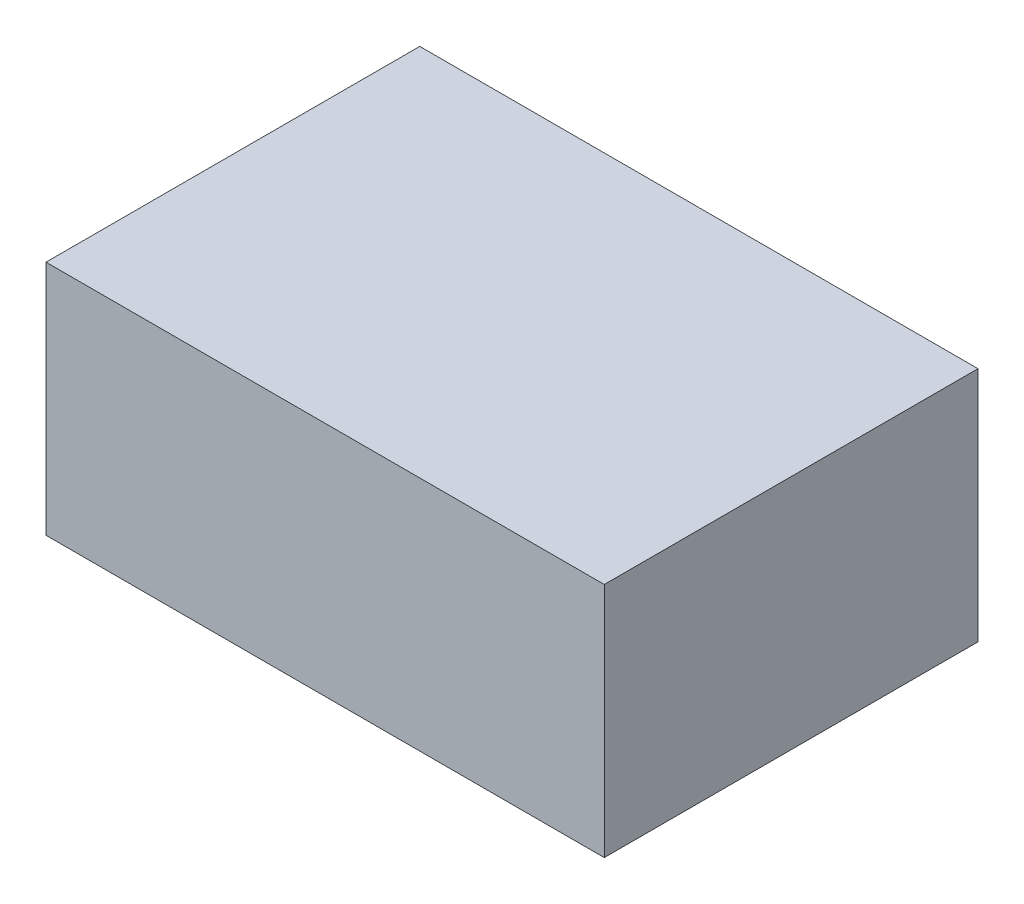
SolidWorks part; units mm, degrees
ref_plane "Front Plane" through (0, 0, 0) normal (0, 0, 1) x (1, 0, 0)
ref_plane "Top Plane" through (0, 0, 0) normal (0, 1, 0) x (1, 0, 0)
ref_plane "Right Plane" through (0, 0, 0) normal (1, 0, 0) x (0, 0, -1)
sketch "Sketch1" plane through (0, 0, 0) normal (0, 1, 0) x (1, 0, 0)
  line L1 (-1.4986, -1.0033) -> (1.4986, -1.0033)
  line L2 (-1.4986, -1.0033) -> (-1.4986, 1.0033)
  line L3 (-1.4986, 1.0033) -> (1.4986, 1.0033)
  line L4 (1.4986, -1.0033) -> (1.4986, 1.0033)
  line L5 (-1.4986, -1.0033) -> (1.4986, 1.0033) construction
  line L6 (-1.4986, 1.0033) -> (1.4986, -1.0033) construction
  point P0 (0, 0)
  dimension "D1" = 2.0066
  dimension "D2" = 2.9972
extrude "Boss-Extrude1" add sketch "Sketch1" along normal blind 1.27
